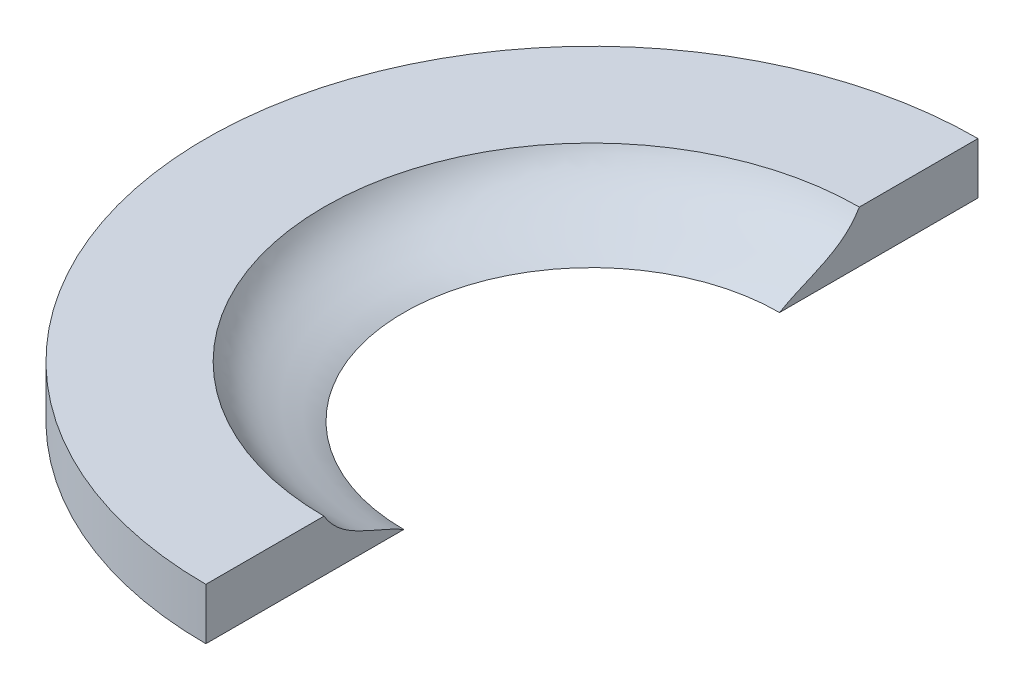
SolidWorks part; units mm, degrees
material "6061-T6 (SS)"
ref_plane "Front Plane" through (0, 0, 0) normal (0, 0, 1) x (1, 0, 0)
ref_plane "Top Plane" through (0, 0, 0) normal (0, 1, 0) x (1, 0, 0)
ref_plane "Right Plane" through (0, 0, 0) normal (1, 0, 0) x (0, 0, -1)
sketch "Sketch1" plane through (0, 0, 0) normal (0, 1, 0) x (1, 0, 0)
  line L5 (0, 0) -> (127.635, 0)
  line L6 (0, 0) -> (0, 127.635)
  line L7 (0, 127.635) -> (127.635, 127.635)
  line L8 (127.635, 0) -> (127.635, 127.635)
  dimension "D1" = 127.635
  dimension "D2" = 127.635
extrude "Boss-Extrude1" add sketch "Sketch1" along normal blind 12.7 contours L5 L8 L7 L6
sketch "Sketch12" plane through (0, 0, 0) normal (0, -1, 0) x (1, 0, 0)
  line L0 (63.8175, 0) -> (63.8175, -127.635) construction
  line L1 (0, 0) -> (127.635, 0) construction
  line L2 (0, -127.635) -> (127.635, -127.635) construction
  line L3 (0, -63.8175) -> (127.635, -63.8175) construction
  line L4 (0, 0) -> (0, -127.635) construction
  line L5 (127.635, 0) -> (127.635, -127.635) construction
  circle A0 centre (63.8175, -63.8175) radius 95.4151
  dimension "D1" = 190.8302
extrude "Boss-Extrude2" add sketch "Sketch12" against normal up to surface (12.7 mm away) contours A0 up to face at (63.8175, 12.7, -63.8175)
sketch "Sketch5" plane through (0, 12.7, 0) normal (0, 1, 0) x (1, 0, 0)
  circle A0 centre (63.8175, 63.8175) radius 46.355
  circle A3 centre (63.8175, 63.8175) radius 95.4151 construction
  dimension "D1" = 92.71
extrude "Cut-Extrude1" cut sketch "Sketch5" against normal blind 9.525
sketch "Sketch14" plane through (0, 12.7, 0) normal (0, -1, 0) x (1, 0, 0)
  line L0 (63.8175, -63.8175) -> (147.6375, -63.8175) construction
  line L1 (0, -19.2087) -> (0, 19.2087) construction
  line L2 (147.6375, -63.8175) -> (152.7175, -63.8175)
  line L3 (136.3808, -105.7742) -> (140.8401, -108.2104)
  circle A0 centre (63.8175, -63.8175) radius 46.355 construction
  arc A2 (147.6375, -63.8175) -> (136.3808, -105.7742) centre (63.8175, -63.8175) cw
  arc A3 (152.7175, -63.8175) -> (140.8401, -108.2104) centre (63.8175, -63.8175) cw
  point P0 (63.8175, -63.8175)
  dimension "D1" = 83.82
  dimension "D2" = 88.9
  dimension "D3" = 46.482
  dimension "D4" = 43.942
ref_plane "Support mirror reference plane" through (0, 4.7625, 0) normal (0, 1, 0) x (1, 0, 0)
sketch "Sketch25" plane through (0, 12.7, 0) normal (0, -1, 0) x (1, 0, 0)
  line L0 (63.8175, -63.8175) -> (123.0872, -4.5478) construction
  line L2 (123.0872, -4.5478) -> (126.6793, -0.9557)
  line L3 (144.7953, -42.1754) -> (149.6712, -40.7448)
  line L5 (63.8175, -63.8175) -> (147.6375, -63.8175) construction
  arc A2 (123.0872, -4.5478) -> (144.7953, -42.1754) centre (63.8175, -63.8175) cw
  arc A3 (126.6793, -0.9557) -> (149.6712, -40.7448) centre (63.8175, -63.8175) cw
  point P0 (63.8175, -63.8175)
  dimension "D1" = 83.82
  dimension "D2" = 88.9
  dimension "D3" = 46.482
  dimension "D4" = 43.942
  dimension "D5" = 45
sketch "Sketch30" plane through (0, 0, 0) normal (0, -1, 0) x (1, 0, 0)
  circle A0 centre (63.8175, -63.8175) radius 85.09
  circle A1 centre (63.8175, -63.8175) radius 79.375
  dimension "D1" = 170.18
  dimension "D2" = 158.75
extrude "Boss-Extrude3" add sketch "Sketch30" along normal blind 12.7
mirror "Mirror1" about plane through (0, 4.7625, 0) normal (0, 1, 0) of "Boss-Extrude3"
sketch "Sketch31" plane through (0, 0, 0) normal (0, -1, 0) x (-1, 0, 0)
  line L0 (-63.8175, -52.481) -> (-63.8175, 177.7216) construction
ref_plane "Plane1" through (0, 0, -148.9075) normal (0, 0, -1) x (-1, 0, 0)
ref_plane "Plane2" through (63.8175, 0, 0) normal (-1, 0, 0) x (0, 0, -1)
sketch "Sketch32" plane through (0, 0, -148.9075) normal (0, 0, -1) x (-1, 0, 0)
  line L4 (-63.8175, -87.3125) -> (-63.8175, 87.3125) construction
  line L5 (-148.9075, 0) -> (21.2725, 0) construction
  line L6 (21.2725, 12.7) -> (-148.9075, 12.7) construction
  circle A0 centre (-63.8175, -6.35) radius 1.3526
  circle A1 centre (-63.8175, 19.05) radius 1.3525
  dimension "D1" = 2.7051
  dimension "D2" = 2.7051
  dimension "D3" = 6.35
  dimension "D4" = 6.35
extrude "Cut-Extrude4" cut sketch "Sketch32" against normal blind 15.24
pattern_circular "CirPattern2" count 12 over 360 about axis through (63.8175, -12.7, -63.8175) along (0, 1, 0) of "Cut-Extrude4"
ref_plane "Plane3" through (0, 0, -63.754) normal (0, 0, 1) x (1, 0, 0)
sketch "Sketch35" plane through (0, 0, -63.754) normal (0, 0, 1) x (1, 0, 0)
  line L3 (110.1725, 12.7) -> (17.4625, 12.7) construction
  line L4 (63.8175, 12.7) -> (129.8575, 12.7)
  line L6 (63.8175, -10.3302) -> (63.8175, 21.6129) construction
  line L8 (110.1725, 0) -> (63.8175, 0)
  line L9 (63.8175, 0) -> (63.8175, 12.7)
  circle A0 centre (63.8175, 19.05) radius 1.3526 construction
  circle A1 centre (63.8175, 19.05) radius 1.3525
  spline S0 degree 3 poles (129.8575, 12.7) (125.5567, 5.3002) (116.9453, 3.9994) (110.1725, 0) knots 0 0 0 0 1 1 1 1
  dimension "D1" = 12.7
  dimension "D2" = 46.355
  dimension "D3" = 66.04
revolve "Cut-Revolve1" cut sketch "Sketch35" angle 360 about L6
sketch "Sketch36" plane through (0, 22.225, 0) normal (0, 1, 0) x (1, 0, 0)
  circle A0 centre (63.8175, 63.8175) radius 115.3121
  circle A1 centre (63.8175, 63.8175) radius 79.375 construction
  circle A2 centre (63.8175, 63.8175) radius 76.2
  dimension "D1" = 152.4
extrude "Cut-Extrude5" cut sketch "Sketch36" against normal through all
sketch "Sketch38" plane through (0, 0, 0) normal (0, -1, 0) x (-1, 0, 0)
  circle A0 centre (-63.8175, 63.8175) radius 95.25
  circle A1 centre (-63.8175, 63.8175) radius 76.2 construction
  circle A2 centre (-63.8175, 63.8175) radius 76.2
  dimension "D1" = 190.5
  dimension "D2" = 152.4
extrude "Boss-Extrude4" add sketch "Sketch38" against normal up to surface (12.7 mm away) up to face at (63.8175, 12.7, -129.794)
sketch "Sketch37" plane through (63.8175, 0, 0) normal (-1, 0, 0) x (0, 0, -1)
  line L1 (165.3317, 47.2836) -> (-43.2842, 47.2836)
  line L2 (165.3317, 47.2836) -> (165.3317, -76.5986)
  line L3 (165.3317, -76.5986) -> (-43.2842, -76.5986)
  line L4 (-43.2842, 47.2836) -> (-43.2842, -76.5986)
extrude "Cut-Extrude6" cut sketch "Sketch37" against normal through all
